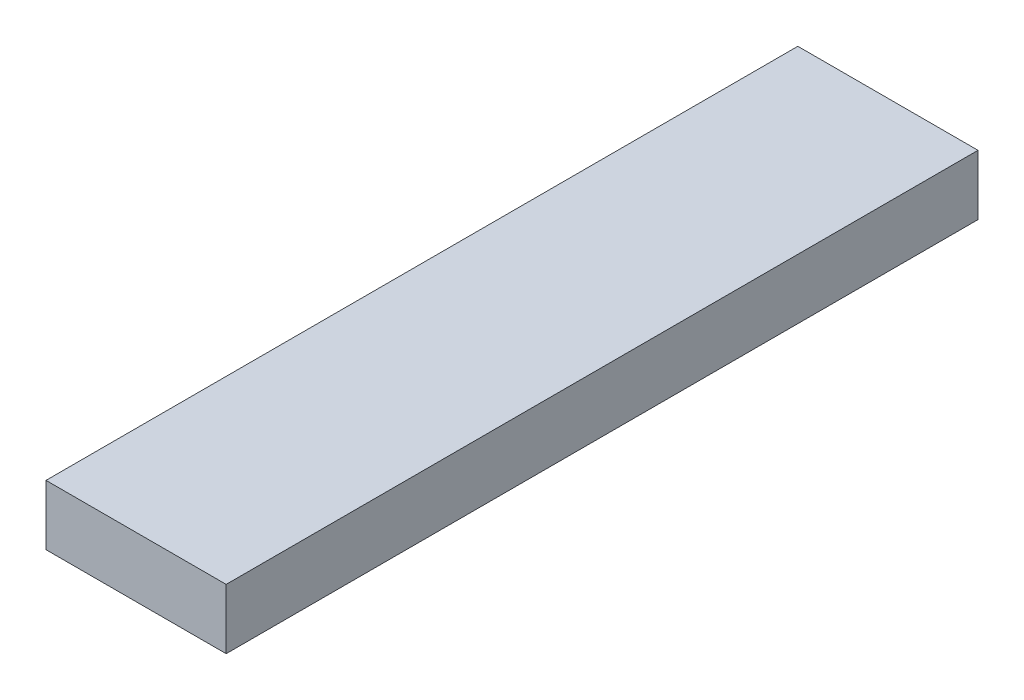
SolidWorks part; units mm, degrees
ref_plane "Front Plane" through (0, 0, 0) normal (0, 0, 1) x (1, 0, 0)
ref_plane "Top Plane" through (0, 0, 0) normal (0, 1, 0) x (1, 0, 0)
ref_plane "Right Plane" through (0, 0, 0) normal (1, 0, 0) x (0, 0, -1)
sketch "Sketch1" plane through (0, 0, 0) normal (0, 0, 1) x (1, 0, 0)
  line L1 (0, 0) -> (38.1, 0)
  line L2 (0, 0) -> (0, 12.7)
  line L3 (0, 12.7) -> (38.1, 12.7)
  line L4 (38.1, 0) -> (38.1, 12.7)
  dimension "D1" = 12.7
  dimension "D2" = 38.1
extrude "Boss-Extrude1" add sketch "Sketch1" along normal blind 159
